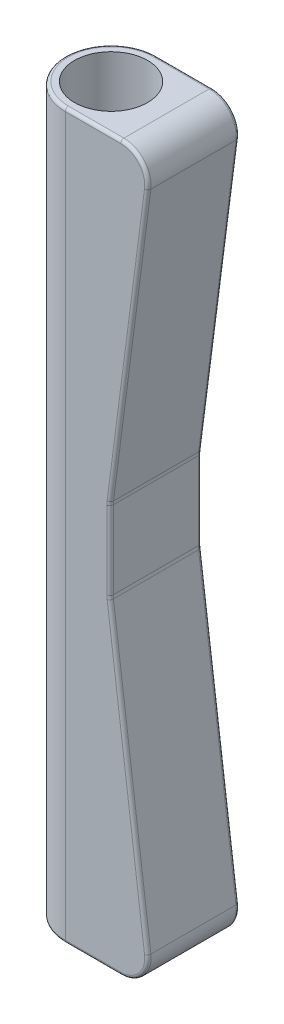
SolidWorks part; units mm, degrees
ref_plane "Front Plane" through (0, 0, 0) normal (0, 0, 1) x (1, 0, 0)
ref_plane "Top Plane" through (0, 0, 0) normal (0, 1, 0) x (1, 0, 0)
ref_plane "Right Plane" through (0, 0, 0) normal (1, 0, 0) x (0, 0, -1)
sketch "Sketch1" plane through (0, 0, 0) normal (0, 1, 0) x (1, 0, 0)
  circle A0 centre (0, 0) radius 11.4125
  circle A1 centre (0, 0) radius 14.2875
  dimension "D1" = 22.825
  dimension "D2" = 28.575
extrude "Boss-Extrude1" add sketch "Sketch1" along normal blind 226.06
ref_plane "Plane1" through (14.2875, 0, 0) normal (1, 0, 0) x (0, 0, -1)
sketch "Sketch2" plane through (14.2875, 0, 0) normal (1, 0, 0) x (0, 0, -1)
  line L1 (14.2875, 0) -> (-14.2875, 0)
  line L2 (14.2875, 0) -> (14.2875, 226.06)
  line L3 (14.2875, 226.06) -> (-14.2875, 226.06)
  line L4 (-14.2875, 0) -> (-14.2875, 226.06)
extrude "Boss-Extrude2" add sketch "Sketch2" along normal blind 12.7 separate body
sketch "Sketch3" plane through (0, 226.06, 0) normal (0, 1, 0) x (1, 0, 0)
  line L0 (14.2875, -14.2875) -> (0, -14.2875)
  line L1 (14.2875, 14.2875) -> (0, 14.2875)
  line L4 (14.2875, 14.2875) -> (14.2875, -14.2875)
  line L5 (14.2875, -14.2875) -> (26.9875, -14.2875)
  line L6 (26.9875, -14.2875) -> (26.9875, 14.2875)
  line L7 (26.9875, 14.2875) -> (14.2875, 14.2875)
  line L9 (14.2875, -14.2875) -> (26.9875, -14.2875)
  line L10 (26.9875, -14.2875) -> (26.9875, 14.2875)
  line L11 (26.9875, 14.2875) -> (14.2875, 14.2875)
  arc A0 (0, -14.2875) -> (0, 14.2875) centre (0, 0) ccw
  dimension "D1" = 0
extrude "Boss-Extrude3" add sketch "Sketch3" against normal through all
sketch "Sketch5" plane through (0, 0, 14.2875) normal (0, 0, 1) x (1, 0, 0)
  line L2 (26.9875, 226.06) -> (13.9875, 125.73)
  line L4 (13.9875, 100.33) -> (26.9875, 0)
  line L8 (26.9875, 0) -> (26.9875, 226.06)
  line L9 (13.9875, 125.73) -> (13.9875, 100.33)
  line L12 (26.9875, 226.06) -> (26.9875, 0)
  dimension "D1" = 25.4
  dimension "D2" = 13
  dimension "D3" = 100.33
extrude "Cut-Extrude1" cut sketch "Sketch5" against normal through all
fillet "Fillet1" radius 8.5 2 edges at (26.9875, 0, 0) (26.9875, 226.06, 0)
fillet "Fillet2" radius 8.5 2 edges at (13.9875, 100.33, 0) (13.9875, 125.73, 0)
fillet "Fillet3" radius 1 20 edges at (23.7, 223.171, 14.2875) (8.6575, 226.06, 14.2875) (-14.2875, 226.06, 0) (8.6575, 226.06, -14.2875) (23.7, 223.171, -14.2875) (19.9013, 171.3708, -14.2875) (14.0051, 125.7289, -14.2875) (13.9875, 113.03, -14.2875) (14.0051, 100.3311, -14.2875) (19.9013, 54.6892, -14.2875) (23.7, 2.889, -14.2875) (8.6575, 0, -14.2875) (-14.2875, 0, 0) (8.6575, 0, 14.2875) (23.7, 2.889, 14.2875) (19.9013, 54.6892, 14.2875) (14.0051, 100.3311, 14.2875) (13.9875, 113.03, 14.2875) (14.0051, 125.7289, 14.2875) (19.9013, 171.3708, 14.2875)
